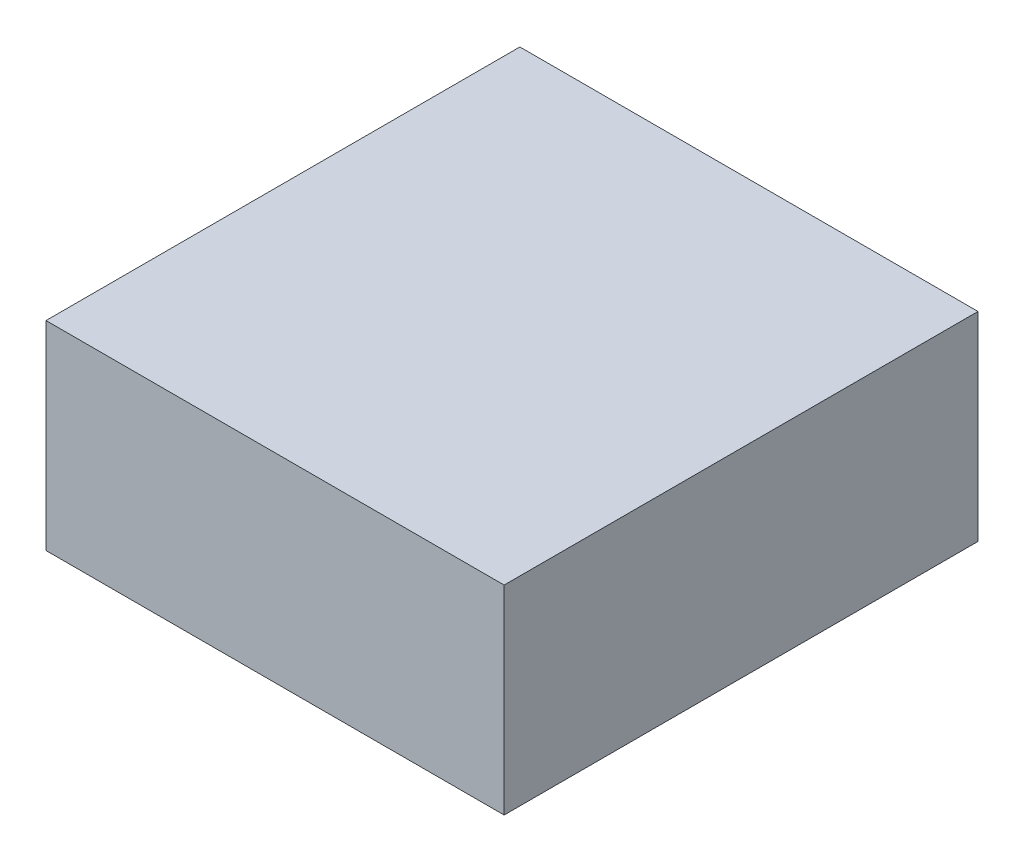
SolidWorks part; units mm, degrees
ref_plane "Front Plane" through (0, 0, 0) normal (0, 0, 1) x (1, 0, 0)
ref_plane "Top Plane" through (0, 0, 0) normal (0, 1, 0) x (1, 0, 0)
ref_plane "Right Plane" through (0, 0, 0) normal (1, 0, 0) x (0, 0, -1)
sketch "Sketch1" plane through (0, 0, 0) normal (0, 0, 1) x (1, 0, 0)
  line L1 (0, 0) -> (110.998, 0)
  line L2 (0, 0) -> (0, 48.26)
  line L3 (0, 48.26) -> (110.998, 48.26)
  line L4 (110.998, 0) -> (110.998, 48.26)
  dimension "D1" = 110.998
  dimension "D2" = 48.26
extrude "Boss-Extrude1" add sketch "Sketch1" along normal blind 114.808
